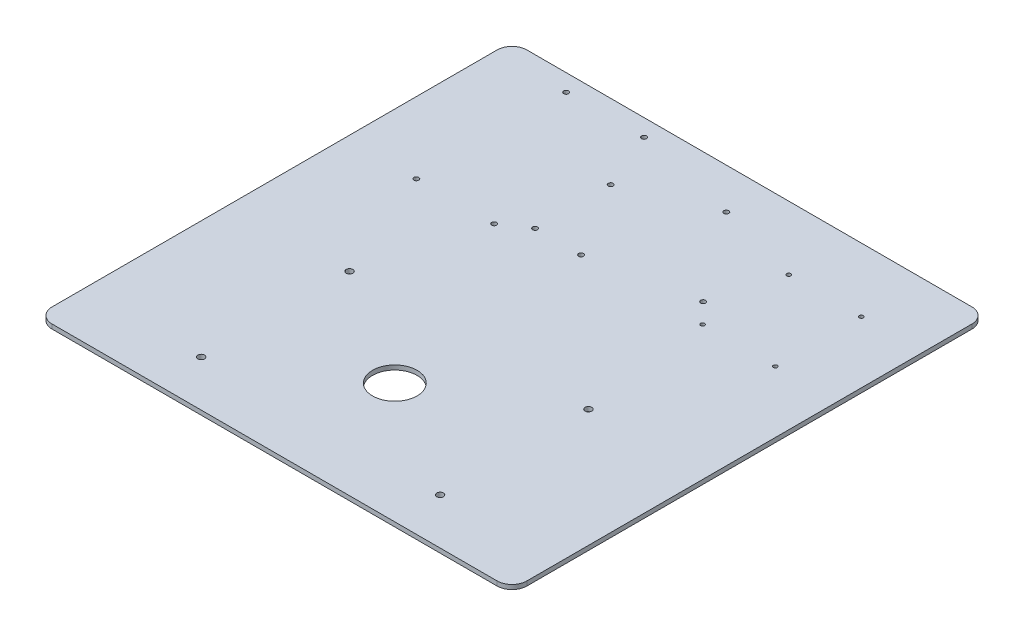
SolidWorks part; units mm, degrees
material "Cedar"
ref_plane "Front Plane" through (0, 0, 0) normal (0, 0, 1) x (1, 0, 0)
ref_plane "Top Plane" through (0, 0, 0) normal (0, 1, 0) x (1, 0, 0)
ref_plane "Right Plane" through (0, 0, 0) normal (1, 0, 0) x (0, 0, -1)
sketch "Sketch1" plane through (0, 0, 0) normal (0, 1, 0) x (1, 0, 0)
  line L0 (111.1, 83.14) -> (111.1, 84.07)
  line L1 (0, 0) -> (111.1, 0)
  line L2 (0, 0) -> (0, 83.14)
  line L3 (0, 83.14) -> (111.1, 83.14)
  line L4 (111.1, 0) -> (111.1, 83.14)
  line L5 (111.1, 0) -> (111.1, -0.93)
  line L6 (111.1, -0.93) -> (167.2, -0.93)
  line L7 (167.2, -0.93) -> (167.2, 84.07)
  line L8 (167.2, 84.07) -> (111.1, 84.07)
  line L9 (169.2, 97.57) -> (-78.8, 97.57)
  line L10 (169.2, -3.43) -> (-78.8, -3.43)
  line L11 (169.2, -14.43) -> (169.2, 97.57)
  line L12 (169.2, 86.57) -> (-78.8, 86.57)
  line L13 (-78.8, -14.43) -> (-78.8, 97.57)
  line L14 (169.2, -14.43) -> (-78.8, -14.43)
  line L16 (-114.8, 103.57) -> (205.2, 103.57)
  line L17 (-114.8, 103.57) -> (-114.8, -216.43)
  line L18 (-114.8, -216.43) -> (205.2, -216.43)
  line L19 (205.2, 103.57) -> (205.2, -216.43)
  line L20 (-54.8, -60.43) -> (145.2, -60.43)
  line L21 (-54.8, -60.43) -> (-54.8, -210.43)
  line L22 (-54.8, -210.43) -> (145.2, -210.43)
  line L23 (145.2, -60.43) -> (145.2, -210.43)
  circle A0 centre (101.6, 16) radius 1.65
  circle A1 centre (2.15, 2.15) radius 1.65
  circle A2 centre (33.15, 2.15) radius 1.65
  circle A3 centre (2.15, 53.15) radius 1.65
  circle A4 centre (57.1, 76.14) radius 1.65
  circle A5 centre (163.7, 2.57) radius 1.35
  circle A6 centre (114.7, 2.57) radius 1.35
  circle A7 centre (163.7, 60.57) radius 1.35
  circle A8 centre (114.7, 60.57) radius 1.35
  circle A9 centre (-14.3, -8.93) radius 1.65
  circle A10 centre (-66.8, -8.93) radius 1.65
  circle A11 centre (-14.3, 92.07) radius 1.65
  circle A12 centre (-66.8, 92.07) radius 1.65
  circle A13 centre (-35.3, -85.43) radius 2.25
  circle A14 centre (125.7, -85.43) radius 2.25
  circle A15 centre (125.7, -185.43) radius 2.25
  circle A16 centre (-35.3, -185.43) radius 2.25
  circle A17 centre (45.2, -135.43) radius 15
  dimension "D6" = 3.3
  dimension "D9" = 3.3
  dimension "D10" = 2
  dimension "D12" = 3.3
  dimension "D14" = 3.3
  dimension "D16" = 3.3
  dimension "D17" = 54
  dimension "D18" = 7
  dimension "D19" = 2.7
  dimension "D20" = 3.5
  dimension "D21" = 3.5
  dimension "D22" = 2.7
  dimension "D23" = 3.5
  dimension "D25" = 2.7
  dimension "D26" = 58
  dimension "D28" = 2.7
  dimension "D36" = 11
  dimension "D37" = 320
  dimension "D38" = 248
  dimension "D39" = 6
  dimension "D40" = 320
  dimension "D41" = 150
  dimension "D44" = 200
  dimension "D46" = 100
  dimension "D30" = 2
  dimension "D35" = 11
  dimension "D33" = 12
  dimension "D34" = 8
  dimension "D47" = 25
  dimension "D49" = 161
  dimension "D52" = 19.5
  dimension "D53" = 100
  dimension "D54" = 75
  dimension "D55" = 19.5
  dimension "D1" = 111.1
  dimension "D2" = 83.14
  dimension "D3" = 0.93
  dimension "D4" = 0.93
  dimension "D5" = 56.1
  dimension "D7" = 9.5
  dimension "D8" = 16
  dimension "D11" = 2.15
  dimension "D13" = 31
  dimension "D15" = 51
  dimension "D24" = 3.6
  dimension "D27" = 58
  dimension "D29" = 2
  dimension "D31" = 90
  dimension "D32" = 2.5
  dimension "D42" = 6
  dimension "D43" = 36
  dimension "D45" = 60
  dimension "D48" = 0
  dimension "D50" = 161
  dimension "D51" = 0
extrude "Boss-Extrude1" add sketch "Sketch1" along normal blind 3
fillet "Fillet1" radius 10 4 edges at (205.2, 1.5, -103.57) (-114.8, 1.5, -103.57) (205.2, 1.5, 216.43) (-114.8, 1.5, 216.43)
